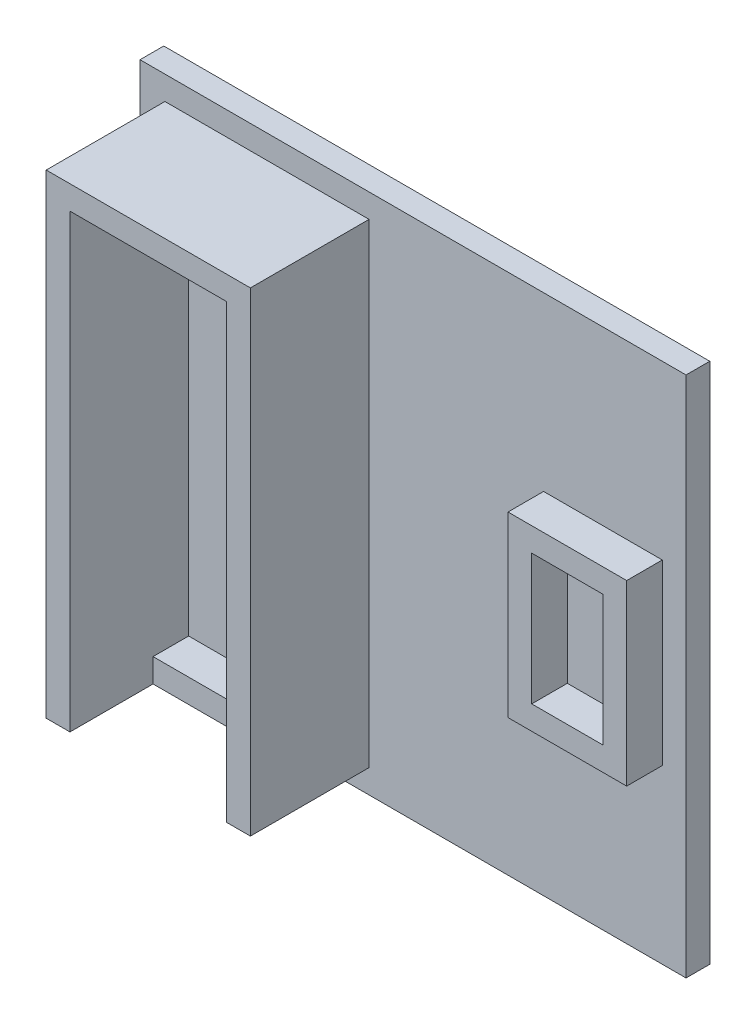
SolidWorks part; units mm, degrees
ref_plane "Plan de face" through (0, 0, 0) normal (0, 0, 1) x (1, 0, 0)
ref_plane "Plan de dessus" through (0, 0, 0) normal (0, 1, 0) x (1, 0, 0)
ref_plane "Plan de droite" through (0, 0, 0) normal (1, 0, 0) x (0, 0, -1)
sketch "Esquisse1" plane through (0, 0, 0) normal (0, 0, 1) x (1, 0, 0)
  line L1 (0, 0) -> (230, 0)
  line L2 (0, 0) -> (0, 220)
  line L3 (0, 220) -> (230, 220)
  line L4 (230, 0) -> (230, 220)
  dimension "D1" = 230
  dimension "D2" = 220
extrude "Boss.-Extru.1" add sketch "Esquisse1" along normal blind 10
sketch "Esquisse2" plane through (0, 0, 10) normal (0, 0, 1) x (1, 0, 0)
  line L1 (10.4872, 10) -> (20.4872, 10)
  line L2 (10.4872, 10) -> (10.4872, 210)
  line L3 (10.4872, 210) -> (20.4872, 210)
  line L4 (20.4872, 10) -> (20.4872, 200)
  line L5 (10.4872, 10) -> (20.4872, 210) construction
  line L6 (10.4872, 210) -> (20.4872, 10) construction
  line L7 (230, 220) -> (0, 220) construction
  line L8 (20.4872, 210) -> (86.4872, 210)
  line L10 (20.4872, 200) -> (86.4872, 200)
  line L12 (86.4872, 210) -> (96.4872, 210)
  line L13 (86.4872, 200) -> (86.4872, 10)
  line L14 (86.4872, 10) -> (96.4872, 10)
  line L15 (96.4872, 210) -> (96.4872, 10)
  point P0 (15.4872, 110)
  dimension "D1" = 10
  dimension "D2" = 200
  dimension "D3" = 10
  dimension "D4" = 66
  dimension "D5" = 10
  dimension "D6" = 10
  dimension "D7" = 200
extrude "Boss.-Extru.2" add sketch "Esquisse2" along normal blind 50
sketch "Esquisse3" plane through (0, 0, 10) normal (0, 0, 1) x (1, 0, 0)
  line L0 (86.4872, 200) -> (86.4872, 10) construction
  line L1 (20.4872, 10) -> (86.4872, 10)
  line L2 (20.4872, 10) -> (20.4872, 20)
  line L3 (20.4872, 20) -> (86.4872, 20)
  line L4 (86.4872, 10) -> (86.4872, 20)
  dimension "D1" = 10
extrude "Boss.-Extru.3" add sketch "Esquisse3" along normal blind 15
sketch "Esquisse4" plane through (0, 0, 10) normal (0, 0, 1) x (1, 0, 0)
  line L0 (230, 220) -> (0, 220) construction
  line L1 (180, 137.5) -> (210, 137.5)
  line L2 (180, 137.5) -> (180, 82.5)
  line L3 (180, 82.5) -> (210, 82.5)
  line L4 (210, 137.5) -> (210, 82.5)
  line L5 (170, 147.5) -> (220, 147.5)
  line L6 (170, 147.5) -> (170, 72.5)
  line L7 (170, 72.5) -> (220, 72.5)
  line L8 (220, 147.5) -> (220, 72.5)
  line L10 (230, 0) -> (230, 220) construction
  dimension "D1" = 30
  dimension "D2" = 55
  dimension "D3" = 10
  dimension "D4" = 10
  dimension "D5" = 10
  dimension "D6" = 10
  dimension "D7" = 72.5
  dimension "D8" = 10
extrude "Boss.-Extru.4" add sketch "Esquisse4" along normal blind 15
